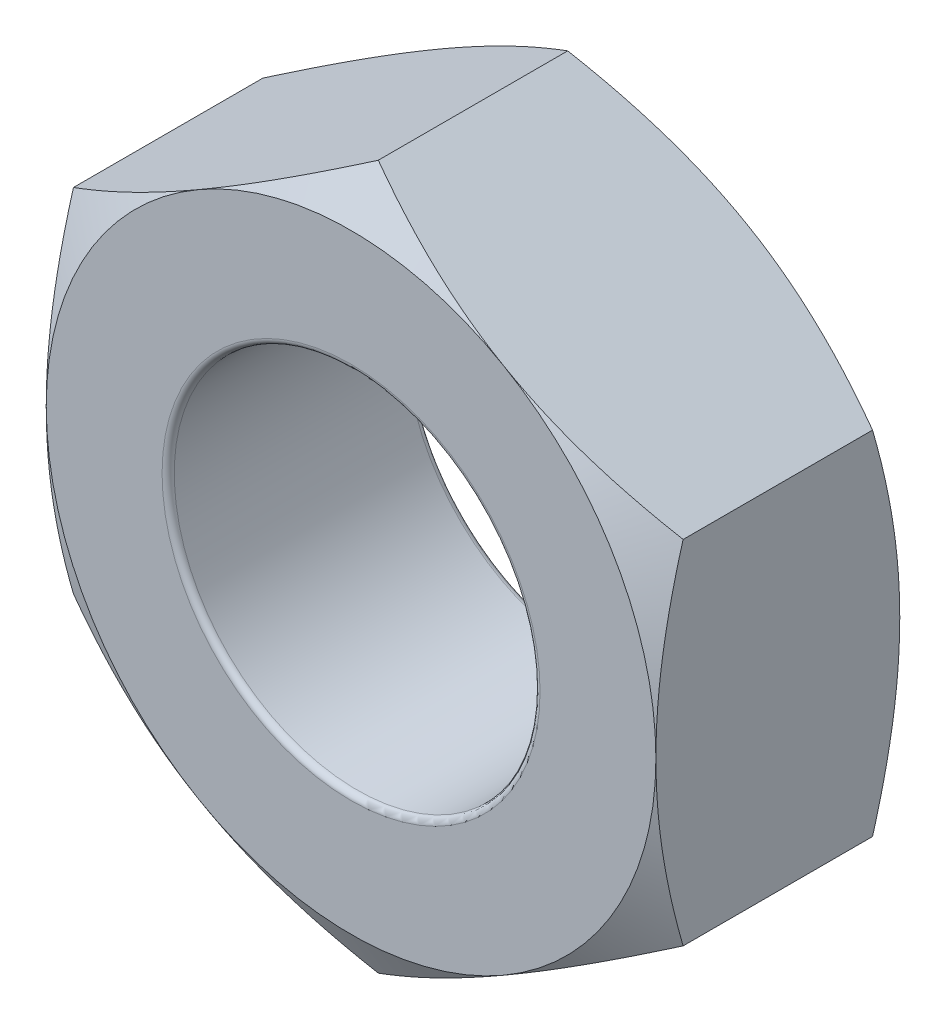
SolidWorks part; units mm, degrees
ref_plane "Front Plane" through (0, 0, 0) normal (0, 0, 1) x (1, 0, 0)
ref_plane "Top Plane" through (0, 0, 0) normal (0, 1, 0) x (1, 0, 0)
ref_plane "Right Plane" through (0, 0, 0) normal (1, 0, 0) x (0, 0, -1)
sketch "Sketch1" plane through (0, 0, 0) normal (0, 0, 1) x (1, 0, 0)
  line L1 (0, -2.8868) -> (2.5, -1.4434)
  line L2 (2.5, -1.4434) -> (2.5, 1.4434)
  line L3 (2.5, 1.4434) -> (0, 2.8868)
  line L4 (0, 2.8868) -> (-2.5, 1.4434)
  line L5 (-2.5, 1.4434) -> (-2.5, -1.4434)
  line L6 (-2.5, -1.4434) -> (0, -2.8868)
  circle A0 centre (0, 0) radius 1.5
  circle A1 centre (0, 0) radius 2.5 construction
  dimension "D1" = 3
  dimension "D2" = 5
extrude "Boss-Extrude1" add sketch "Sketch1" along normal blind 2
sketch "Sketch2" plane through (0, 0, 2) normal (0, 0, 1) x (1, 0, 0)
  circle A0 centre (0, 0) radius 2.5 construction
  circle A1 centre (0, 0) radius 2.5
extrude "Cut-Extrude1" cut sketch "Sketch2" against normal blind 2 draft 60 flip side to cut
sketch "Sketch3" plane through (0, 0, 0) normal (0, 0, -1) x (-1, 0, 0)
  circle A1 centre (0, 0) radius 2.5
  circle A2 centre (0, 0) radius 2.5
  dimension "D1" = 0
extrude "Cut-Extrude2" cut sketch "Sketch3" against normal blind 2 draft 60 flip side to cut
fillet "Fillet1" radius 0.05 2 edges at (1.5, 0, 0) (1.5, 0, 2)
